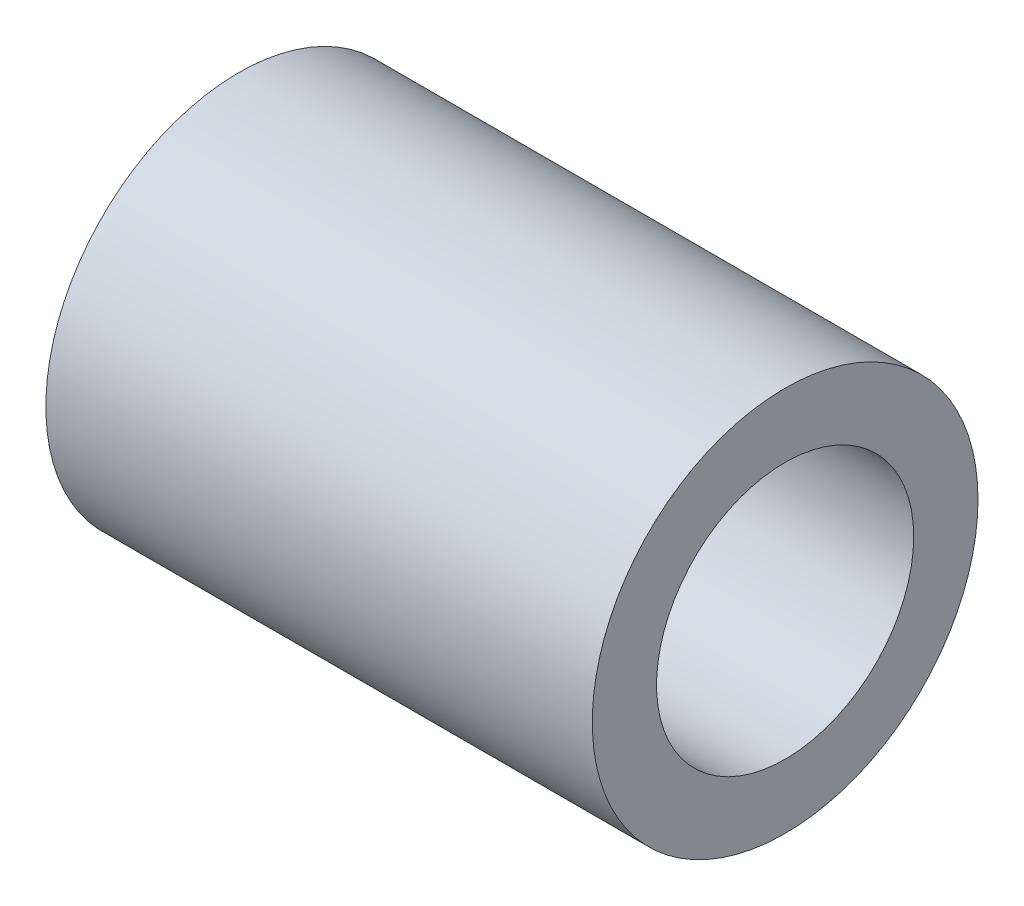
SolidWorks part; units mm, degrees
ref_plane "Alzado" through (0, 0, 0) normal (0, 0, 1) x (1, 0, 0)
ref_plane "Planta" through (0, 0, 0) normal (0, 1, 0) x (1, 0, 0)
ref_plane "Vista lateral" through (0, 0, 0) normal (1, 0, 0) x (0, 0, -1)
sketch "Croquis1" plane through (0, 0, 0) normal (1, 0, 0) x (0, 0, -1)
  circle A0 centre (0, 0) radius 6
  circle A1 centre (0, 0) radius 4
  dimension "D1" = 12
  dimension "D2" = 8
extrude "Saliente-Extruir1" add sketch "Croquis1" along normal blind 17
